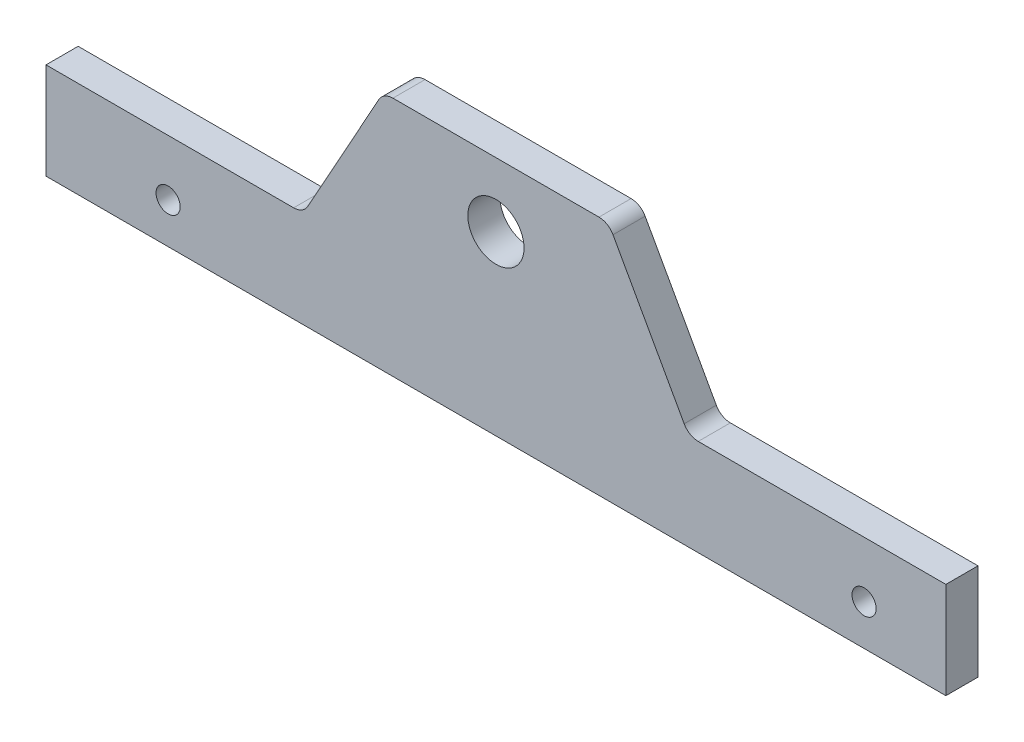
SolidWorks part; units mm, degrees
ref_plane "Front Plane" through (0, 0, 0) normal (0, 0, 1) x (1, 0, 0)
ref_plane "Top Plane" through (0, 0, 0) normal (0, 1, 0) x (1, 0, 0)
ref_plane "Right Plane" through (0, 0, 0) normal (1, 0, 0) x (0, 0, -1)
sketch "Sketch1" plane through (0, 0, 0) normal (0, 0, 1) x (1, 0, 0)
  line L0 (-88.9, 0) -> (-39.9682, 0)
  line L1 (-37.1927, 1.6331) -> (-23.1323, 26.9419)
  line L2 (-20.3568, 28.575) -> (20.3568, 28.575)
  line L3 (0, 28.575) -> (0, 0) construction
  line L4 (37.1927, 1.6331) -> (23.1323, 26.9419)
  line L5 (88.9, 0) -> (39.9682, 0)
  line L6 (-88.9, 0) -> (-88.9, -19.05)
  line L7 (-88.9, -19.05) -> (88.9, -19.05)
  line L8 (88.9, -19.05) -> (88.9, 0)
  arc A0 (-23.1323, 26.9419) -> (-20.3568, 28.575) centre (-20.3568, 25.4) cw
  arc A1 (23.1323, 26.9419) -> (20.3568, 28.575) centre (20.3568, 25.4) ccw
  arc A2 (37.1927, 1.6331) -> (39.9682, 0) centre (39.9682, 3.175) ccw
  arc A3 (-39.9682, 0) -> (-37.1927, 1.6331) centre (-39.9682, 3.175) ccw
  circle A4 centre (0, 15.875) radius 5.5563
  point P13 (-22.225, 28.575)
  point P17 (22.225, 28.575)
  point P21 (38.1, 0)
  point P25 (-38.1, 0)
  dimension "D6" = 3.175
  dimension "D7" = 12.7
  dimension "D8" = 11.1125
  dimension "D1" = 76.2
  dimension "D2" = 177.8
  dimension "D3" = 28.575
  dimension "D4" = 44.45
  dimension "D5" = 19.05
extrude "Boss-Extrude1" add sketch "Sketch1" along normal mid plane 6.35
sketch "Sketch2" plane through (0, 0, 3.175) normal (0, 0, 1) x (1, 0, 0)
  line L0 (-39.9682, 0) -> (-88.9, 0) construction
  circle A0 centre (-64.77, -11.049) radius 2.3876
  circle A1 centre (72.7456, -11.049) radius 2.3876
  dimension "D1" = 11.049
  dimension "D2" = 64.77
  dimension "D3" = 4.7752
  dimension "D4" = 137.5156
extrude "Cut-Extrude1" cut sketch "Sketch2" against normal through all
